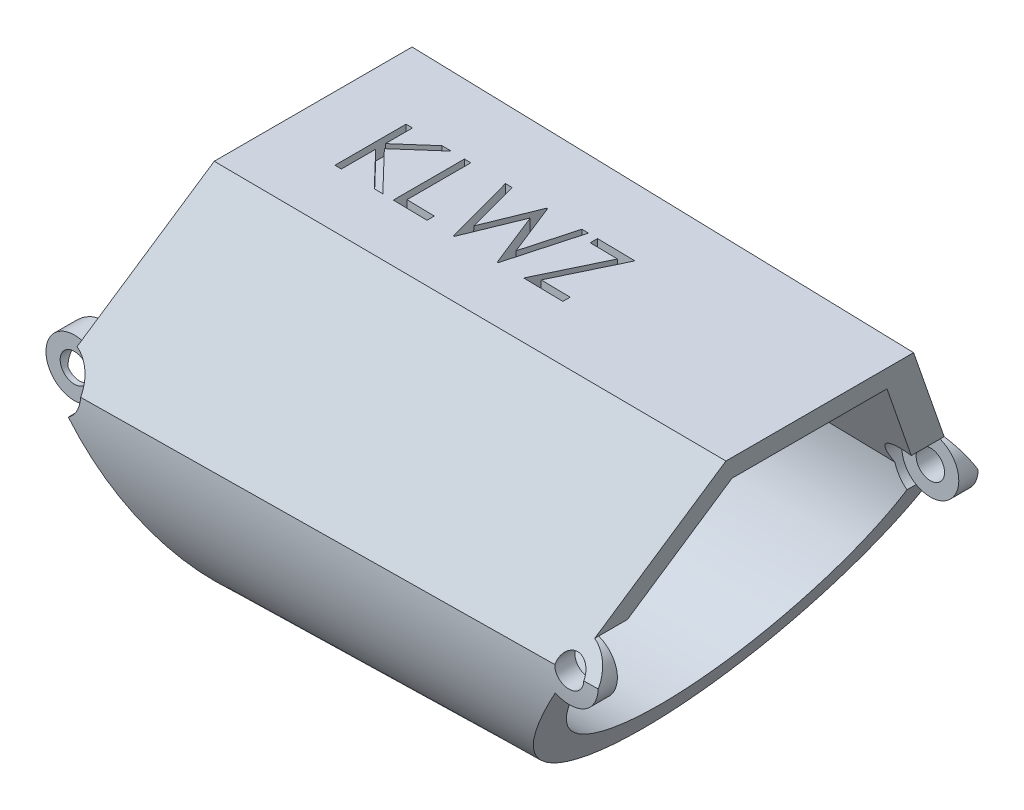
SolidWorks part; units mm, degrees
material "1060 Alloy"
ref_plane "Front Plane" through (0, 0, 0) normal (0, 0, 1) x (1, 0, 0)
ref_plane "Top Plane" through (0, 0, 0) normal (0, 1, 0) x (1, 0, 0)
ref_plane "Right Plane" through (0, 0, 0) normal (1, 0, 0) x (0, 0, -1)
sketch "Sketch1" plane through (0, 0, 0) normal (1, 0, 0) x (0, 0, -1)
  line L0 (-4.445, 0) -> (4.445, 0)
  line L1 (4.445, 0) -> (8.89, -7.699)
  line L2 (-4.445, 0) -> (-8.89, -7.699)
  arc A0 (-8.89, -7.699) -> (8.89, -7.699) centre (0, -8.207) ccw
  point P6 (0, 0)
  dimension "D4" = 0.508
  dimension "D1" = 8.89
  dimension "D2" = 120
  dimension "D3" = 120
extrude "Boss-Extrude1" add sketch "Sketch1" along normal blind 25.4 draft 1
shell "Shell1" thickness 1.27
sketch "Sketch4" plane through (0, 0, 0) normal (-1, 0, 0) x (0, 0, 1)
  line L0 (-8.1568, -6.429) -> (-6.6901, -6.429)
  line L1 (-8.89, -7.699) -> (-4.445, 0) construction
  line L2 (-7.6329, -8.062) -> (-3.7117, -1.2702) construction
  line L3 (-6.6901, -6.429) -> (-7.6329, -8.062)
  line L4 (-8.1568, -6.429) -> (-8.89, -7.699)
  line L5 (-8.8718, -8.969) -> (-7.5962, -8.969)
  line L6 (0, -11.0679) -> (0, -5.396) construction
  line L7 (8.8718, -8.969) -> (7.5962, -8.969)
  line L8 (8.1568, -6.429) -> (8.89, -7.699)
  line L9 (6.6901, -6.429) -> (7.6329, -8.062)
  line L10 (8.1568, -6.429) -> (6.6901, -6.429)
  arc A0 (-8.89, -7.699) -> (-8.8718, -8.969) centre (0, -8.207) ccw
  arc A1 (-8.89, -7.699) -> (8.89, -7.699) centre (0, -8.207) ccw construction
  arc A2 (-7.6329, -8.062) -> (7.6329, -8.062) centre (0, -8.207) ccw construction
  arc A3 (-7.6329, -8.062) -> (-7.5962, -8.969) centre (0, -8.207) ccw
  arc A4 (7.6329, -8.062) -> (7.5962, -8.969) centre (0, -8.207) cw
  arc A5 (8.89, -7.699) -> (8.8718, -8.969) centre (0, -8.207) cw
  dimension "D1" = 2.54
  dimension "D2" = 1.27
extrude "Boss-Extrude2" add sketch "Sketch4" along normal blind 1.27
sketch "Sketch2" plane through (0, 0, 0) normal (0, 0, 1) x (1, 0, 0)
  line L2 (0, -17.1115) -> (25.4, -16.6681) construction
  line L5 (25.4, -0.4434) -> (23.1514, -6.6213)
  line L6 (22.0821, -8.9145) -> (17.5262, -16.8055)
  line L7 (17.5262, -16.8055) -> (25.4, -16.6681)
  line L8 (25.4, -16.6681) -> (25.4, -0.4434)
  line L15 (-2.1296, -17.4852) -> (-2.1296, 2.0873)
  line L16 (-2.1296, 2.0873) -> (3.5619, 2.0873)
  line L17 (3.5619, 2.0873) -> (0.4344, -6.5056)
  line L18 (0.7284, -8.7393) -> (6.8524, -17.4852)
  line L19 (6.8524, -17.4852) -> (-2.1296, -17.4852)
  arc A0 (0.7284, -8.7393) -> (0.4344, -6.5056) centre (0, -7.699) cw
  arc A1 (23.1514, -6.6213) -> (22.0821, -8.9145) centre (22.7171, -7.8147) cw
  circle A2 centre (0, -7.699) radius 0.635
  circle A3 centre (22.7171, -7.8147) radius 0.635
  spline S0 degree 3 poles (25.4, -7.8282) (16.9333, -7.7855) (8.4667, -7.7425) (0, -7.699) knots 0 0 0 0 0.025404 0.025404 0.025404 0.025404 construction
  point P9 (-2.1296, -7.699)
  point P22 (0, 0)
  point P23 (0, 0)
  dimension "D5" = 1.27
  dimension "D6" = 1.27
  dimension "D1" = 20
  dimension "D2" = 35
  dimension "D3" = 20
  dimension "D4" = 30
extrude "Cut-Extrude1" cut sketch "Sketch2" against normal through all both and the other way through all
ref_plane "Plane1" through (0, 0, 7.874) normal (0, 0, 1) x (1, 0, 0)
sketch "Sketch5" plane through (0, 0, 7.874) normal (0, 0, 1) x (1, 0, 0)
  circle A0 centre (0, -7.699) radius 1.27
  dimension "D1" = 2.54
extrude "Cut-Extrude3" cut sketch "Sketch5" along normal blind 7.874
mirror "Mirror1" about plane through (0, 0, 0) normal (0, 0, 1) of "Cut-Extrude3"
sketch "Sketch6" plane through (0, 0, 0) normal (0, 0, 1) x (1, 0, 0)
  circle A0 centre (22.7171, -7.8147) radius 1.27
extrude "Cut-Extrude4" cut sketch "Sketch6" against normal blind 7.62 and the other way blind 7.62
sketch "Sketch3" plane through (0, 0, 0) normal (0.0175, 0.9998, 0) x (0.9998, -0.0175, 0)
  text T0 "KLWZ" font "Century Gothic" height in points 12
extrude "Cut-Extrude2" cut sketch "Sketch3" against normal blind 0.762
